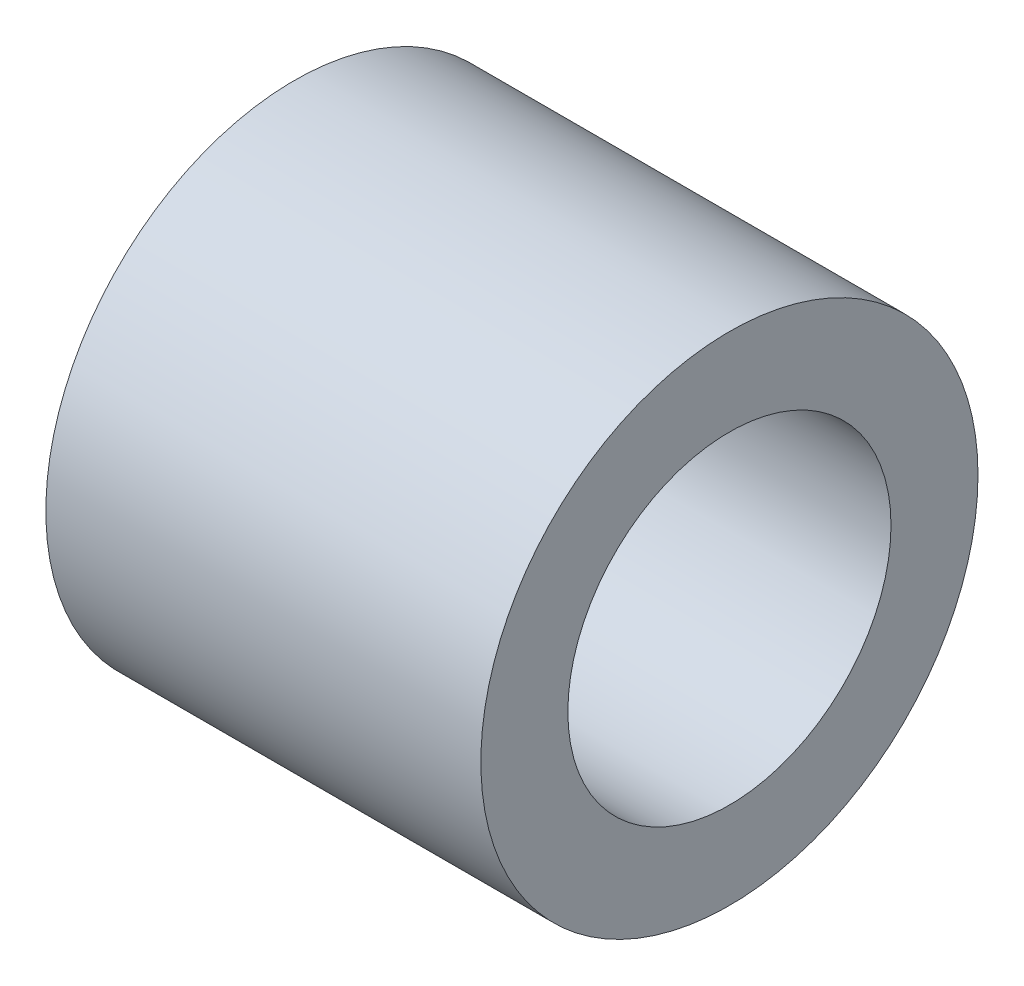
SolidWorks part; units mm, degrees
ref_plane "Front Plane" through (0, 0, 0) normal (0, 0, 1) x (1, 0, 0)
ref_plane "Top Plane" through (0, 0, 0) normal (0, 1, 0) x (1, 0, 0)
ref_plane "Right Plane" through (0, 0, 0) normal (1, 0, 0) x (0, 0, -1)
sketch "Sketch1" plane through (0, 0, 0) normal (1, 0, 0) x (0, 0, -1)
  circle A0 centre (0, 0) radius 4
  circle A1 centre (0, 0) radius 2.6
  dimension "D1" = 8
  dimension "D2" = 5.2
extrude "Boss-Extrude1" add sketch "Sketch1" along normal blind 7
